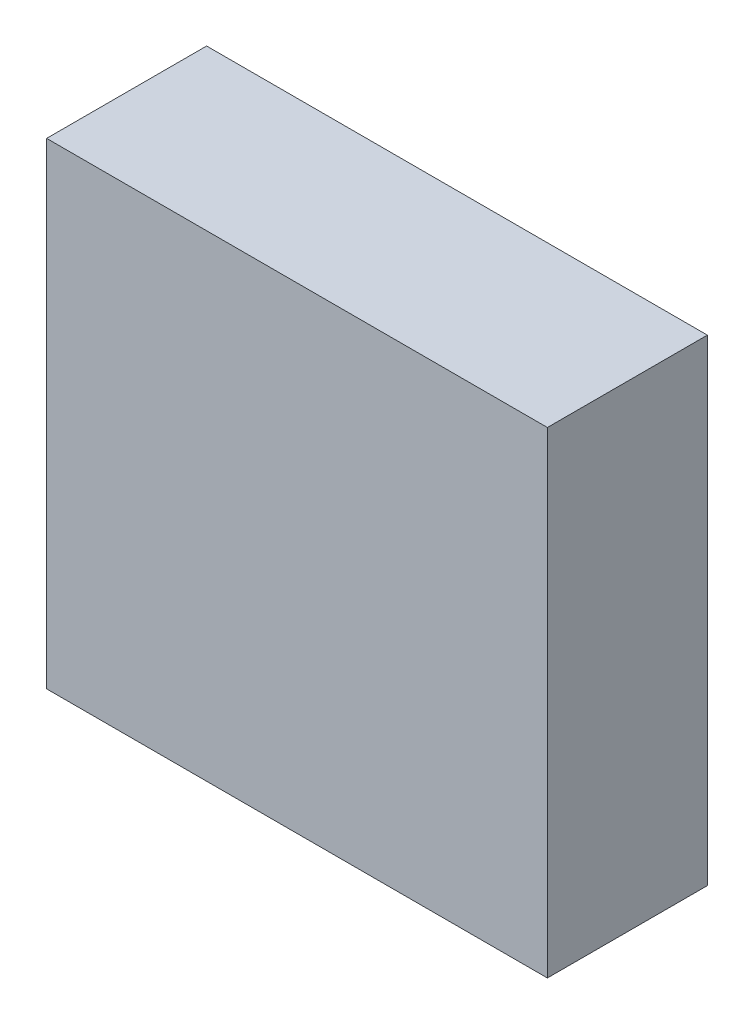
SolidWorks part; units mm, degrees
ref_plane "Front Plane" through (0, 0, 0) normal (0, 0, 1) x (1, 0, 0)
ref_plane "Top Plane" through (0, 0, 0) normal (0, 1, 0) x (1, 0, 0)
ref_plane "Right Plane" through (0, 0, 0) normal (1, 0, 0) x (0, 0, -1)
sketch "Sketch1" plane through (0, 0, 0) normal (0, 0, 1) x (1, 0, 0)
  line L1 (-39.751, 37.846) -> (39.751, 37.846)
  line L2 (-39.751, 37.846) -> (-39.751, -37.846)
  line L3 (-39.751, -37.846) -> (39.751, -37.846)
  line L4 (39.751, 37.846) -> (39.751, -37.846)
  line L5 (-39.751, 37.846) -> (39.751, -37.846) construction
  line L6 (-39.751, -37.846) -> (39.751, 37.846) construction
  point P0 (0, 0)
  dimension "D1" = 79.502
  dimension "D2" = 75.692
extrude "Boss-Extrude1" add sketch "Sketch1" along normal blind 25.4
